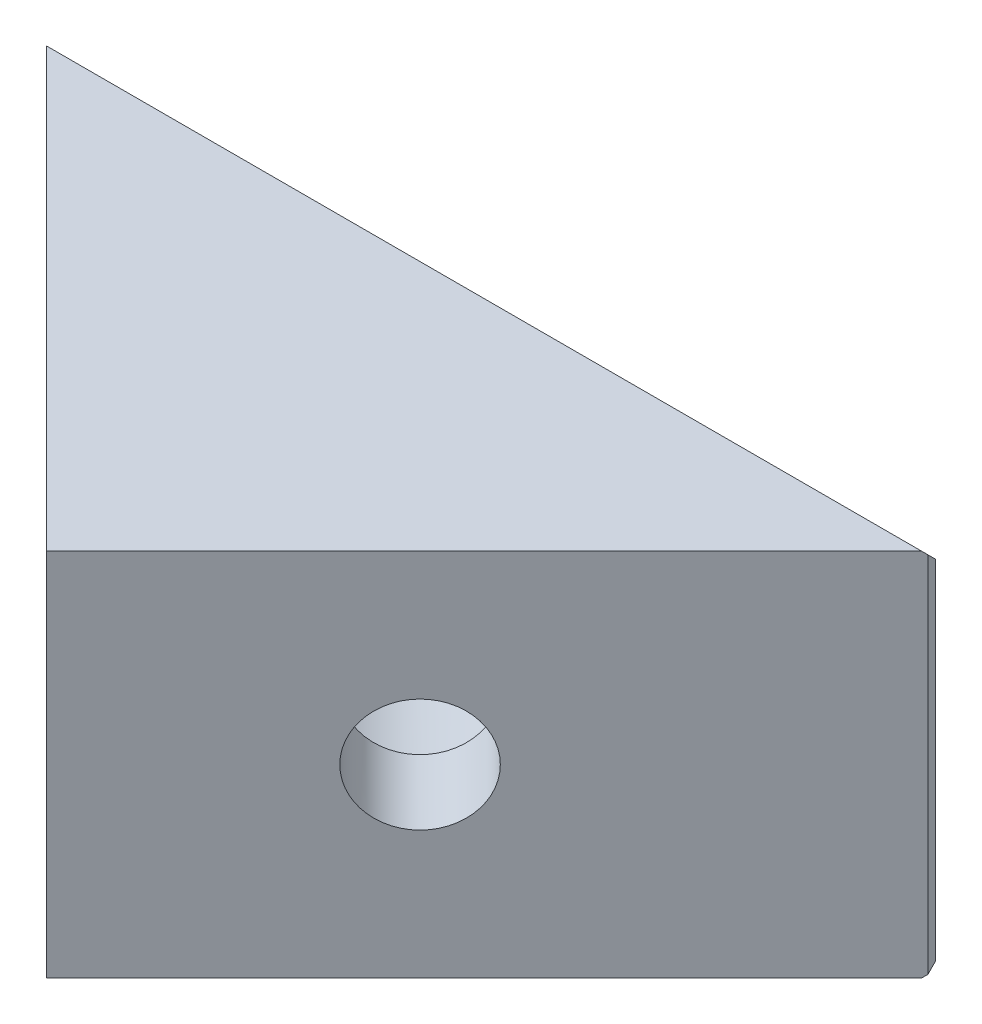
SolidWorks part; units mm, degrees
material "Custom Plastic"
ref_plane "Front Plane" through (0, 0, 0) normal (0, 0, 1) x (1, 0, 0)
ref_plane "Top Plane" through (0, 0, 0) normal (0, 1, 0) x (1, 0, 0)
ref_plane "Right Plane" through (0, 0, 0) normal (1, 0, 0) x (0, 0, -1)
sketch "Sketch1" plane through (0, 0, 0) normal (0, 1, 0) x (1, 0, 0)
  line L0 (0, 0) -> (33.9411, 0)
  line L1 (33.9411, 0) -> (16.9706, -16.9706)
  line L2 (16.9706, -16.9706) -> (0, 0)
  line L3 (16.9706, -16.9706) -> (16.9706, 0) construction
  dimension "D1" = 24
extrude "Boss-Extrude1" add sketch "Sketch1" along normal blind 14
sketch "Sketch2" plane through (0, 0, 0) normal (-0.7071, 0, 0.7071) x (0.7071, 0, 0.7071)
  line L0 (24, 7) -> (14, 7) construction
  line L1 (24, 14) -> (24, 0) construction
  circle A0 centre (14, 7) radius 2.15
  dimension "D1" = 4.3
  dimension "D2" = 10
extrude "Cut-Extrude1" cut sketch "Sketch2" against normal through all
sketch "Sketch3" plane through (0, 0, 0) normal (-0.7071, 0, 0.7071) x (0.7071, 0, 0.7071)
  circle A0 centre (14, 7) radius 4.3
  circle A1 centre (14, 7) radius 2.15 construction
  dimension "D1" = 8.6
extrude "Cut-Extrude2" cut sketch "Sketch3" against normal through all from offset 5.6 offset against normal yes
ref_plane "Plane1" through (16.9706, 0, 0) normal (1, 0, 0) x (0, 0, -1)
mirror "Mirror1" about plane through (16.9706, 0, 0) normal (1, 0, 0) of "Cut-Extrude2", "Cut-Extrude1"
chamfer "Chamfer1" distance 2.1 angle 45 2 edges at (21.6021, 7, 4.4194) (15.3796, 7, 7.46)
chamfer "Chamfer2" distance 0.4 angle 45 4 edges at (33.9411, 7, 0) (16.9706, 14, 0) (0, 7, 0) (16.9706, 0, 0)
fillet "Fillet1" radius 0.5 2 edges at (8.061, 7, 0) (25.8801, 7, 0)
equation "\"y-cross-rib-thickness\"=6"
equation "\"y-rib-thickness\"=6"
equation "\"bed-plate-thickness\"=6"
equation "\"x-plate-thickness\"=5"
equation "\"rod-diameter\"=12"
equation "\"t-nut-hole-diameter\"=3"
equation "\"y-plate-thickness\"=5"
equation "\"enclosure-thickness\"=0.6"
equation "\"M3-Clearance\"=3.3"
equation "\"M4-Clearance\"=4.3"
equation "\"M5-Clearance\"=5.3"
equation "\"M6-Clearance\"=6.3"
equation "\"M8-Clearance\"=8.3"
equation "\"623-Bearing-Dia\"=11.2"
